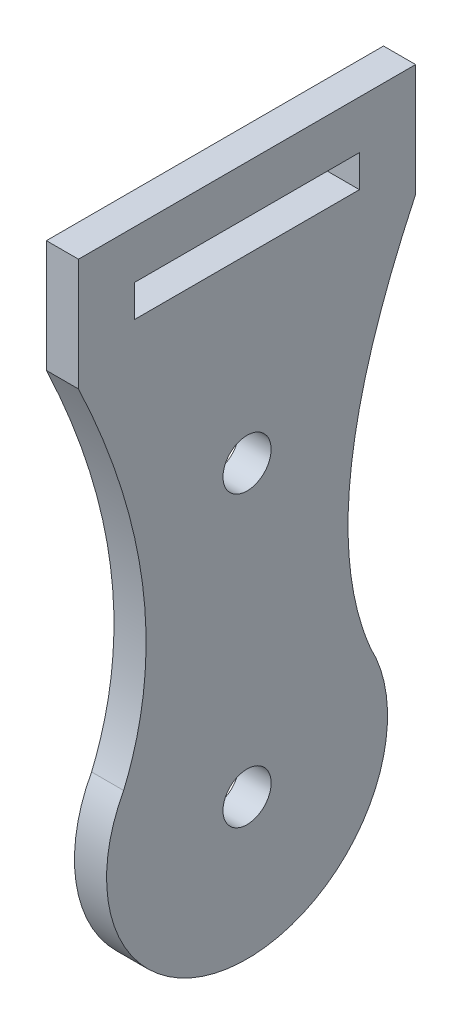
SolidWorks part; units mm, degrees
material "Plástico personalizado"
ref_plane "Plano frontal" through (0, 0, 0) normal (0, 0, 1) x (1, 0, 0)
ref_plane "Plano superior" through (0, 0, 0) normal (0, 1, 0) x (1, 0, 0)
ref_plane "Plano direito" through (0, 0, 0) normal (1, 0, 0) x (0, 0, -1)
sketch "Esboço1" plane through (0, 0, 0) normal (1, 0, 0) x (0, 0, -1)
  line L0 (-10.5, 34.25) -> (0, 34.25)
  line L2 (-10.5, 34.25) -> (-10.5, 27.25)
  line L3 (0, 34.25) -> (0, -8.75)
  arc A0 (-7.6848, 4.184) -> (0, -8.75) centre (0, 0) ccw
  spline S0 degree 2 poles (-10.5, 27.25) (-3.865, 13.2514) (-7.6848, 4.184) knots 0 0 0 0.912496 0.912496 0.912496
  dimension "D1" = 17.5
  dimension "D2" = 10.5
  dimension "D3" = 43
  dimension "D4" = 7
extrude "Ressalto-extrusão1" add sketch "Esboço1" along normal blind 2
mirror "Espelhar1" about plane through (2, 34.25, 0) normal (0, 0, 1) of "Ressalto-extrusão1"
sketch "Esboço2" plane through (2, 0, 0) normal (1, 0, 0) x (0, 0, -1)
  line L1 (-7, 31.25) -> (7, 31.25)
  line L2 (-7, 31.25) -> (-7, 29.25)
  line L3 (-7, 29.25) -> (7, 29.25)
  line L4 (7, 31.25) -> (7, 29.25)
  line L5 (-7, 31.25) -> (7, 29.25) construction
  line L6 (-7, 29.25) -> (7, 31.25) construction
  circle A0 centre (0, 18) radius 1.5
  arc A1 (-7.6848, 4.184) -> (7.6848, 4.184) centre (0, 0) ccw construction
  circle A12 centre (0, 0) radius 1.5
  point P0 (0, 30.25)
  point P11 (0, -8.75)
  point P21 (-11.6412, -4.5532)
  point P26 (8.4604, -5.3312)
  dimension "D3" = 18
  dimension "D4" = 38
  dimension "D8" = 3
  dimension "D1" = 2
  dimension "D2" = 14
extrude "Corte-extrusão1" cut sketch "Esboço2" against normal through all
